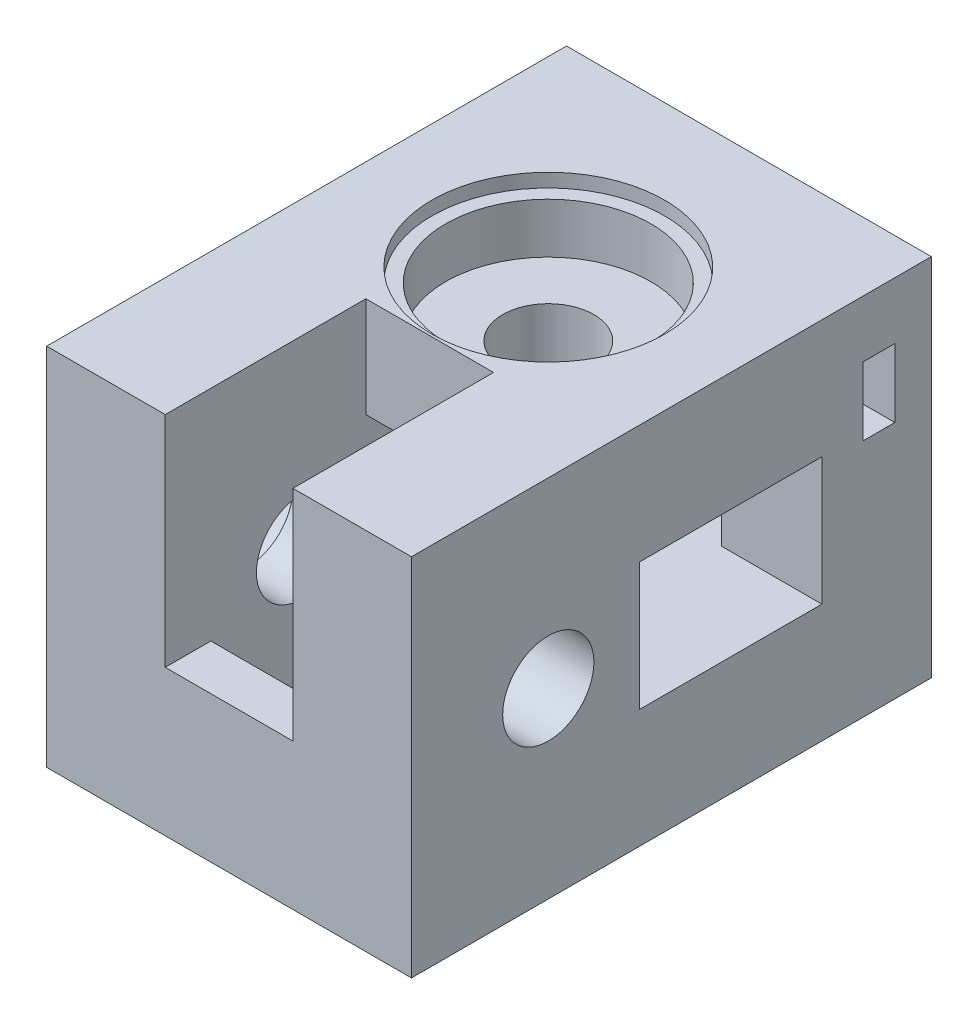
SolidWorks part; units mm, degrees
ref_plane "Plan de face" through (0, 0, 0) normal (0, 0, 1) x (1, 0, 0)
ref_plane "Plan de dessus" through (0, 0, 0) normal (0, 1, 0) x (1, 0, 0)
ref_plane "Plan de droite" through (0, 0, 0) normal (1, 0, 0) x (0, 0, -1)
sketch "Esquisse1" plane through (0, 0, 0) normal (0, 0, 1) x (1, 0, 0)
  line L1 (-40, 40) -> (0, 40)
  line L2 (-40, 40) -> (-40, 0)
  line L3 (-40, 0) -> (0, 0)
  line L4 (0, 40) -> (0, 0)
  dimension "D1" = 40
  dimension "D2" = 40
extrude "Boss.-Extru.1" add sketch "Esquisse1" along normal blind 50
sketch "Esquisse2" plane through (0, 40, 0) normal (0, 1, 0) x (1, 0, 0)
  line L0 (0, 0) -> (-40, 0) construction
  line L1 (-40, -50) -> (-40, 0) construction
  circle A0 centre (-20, -15) radius 5
  dimension "D1" = 10
  dimension "D2" = 15
  dimension "D3" = 20
extrude "Enlèv. mat.-Extru.1" cut sketch "Esquisse2" against normal through all
sketch "Esquisse3" plane through (-40, 0, 0) normal (-1, 0, 0) x (0, 0, 1)
  line L0 (50, 40) -> (50, 0) construction
  line L1 (50, 40) -> (0, 40) construction
  circle A0 centre (35, 20) radius 5
  dimension "D1" = 10
  dimension "D2" = 15
  dimension "D3" = 20
extrude "Enlèv. mat.-Extru.2" cut sketch "Esquisse3" against normal through all
sketch "Esquisse4" plane through (-40, 0, 0) normal (-1, 0, 0) x (0, 0, 1)
  line L1 (22, 27) -> (0, 27)
  line L2 (22, 27) -> (22, 13)
  line L3 (22, 13) -> (0, 13)
  line L4 (0, 27) -> (0, 13)
  line L5 (0, 40) -> (0, 0) construction
  line L6 (50, 0) -> (0, 0) construction
  line L7 (50, 40) -> (0, 40) construction
  dimension "D1" = 14
  dimension "D2" = 22
  dimension "D3" = 0
  dimension "D4" = 13
  dimension "D5" = 13
extrude "Enlèv. mat.-Extru.3" cut sketch "Esquisse4" against normal blind 29
sketch "Esquisse5" plane through (0, 0, 0) normal (0, -1, 0) x (1, 0, 0)
  line L0 (-40, 50) -> (0, 50) construction
  line L1 (-13, 25) -> (-27, 25)
  line L2 (-13, 25) -> (-13, 45)
  line L3 (-13, 45) -> (-27, 45)
  line L4 (-27, 25) -> (-27, 45)
  line L5 (-40, 50) -> (-40, 0) construction
  dimension "D1" = 20
  dimension "D2" = 5
  dimension "D3" = 14
  dimension "D4" = 13
extrude "Enlèv. mat.-Extru.4" cut sketch "Esquisse5" against normal blind 29
sketch "Esquisse6" plane through (0, 0, 0) normal (1, 0, 0) x (0, 0, -1)
  line L1 (-5, 27) -> (-25, 27)
  line L2 (0, 0) -> (0, 40) construction
  line L3 (-5, 13) -> (-25, 13)
  line L4 (-25, 27) -> (-25, 13)
  line L5 (-50, 0) -> (0, 0) construction
  line L6 (-5, 27) -> (-5, 13)
  dimension "D1" = 14
  dimension "D2" = 5
  dimension "D3" = 13
  dimension "D4" = 20
extrude "Enlèv. mat.-Extru.5" cut sketch "Esquisse6" against normal blind 24
sketch "Esquisse7" plane through (0, 40, 0) normal (0, 1, 0) x (1, 0, 0)
  line L0 (0, -50) -> (-40, -50) construction
  line L1 (-27, -50) -> (-13, -50)
  line L2 (-27, -50) -> (-27, -28)
  line L3 (-27, -28) -> (-13, -28)
  line L4 (-13, -50) -> (-13, -28)
  line L5 (-40, -50) -> (-40, 0) construction
  dimension "D1" = 14
  dimension "D2" = 22
  dimension "D3" = 13
extrude "Enlèv. mat.-Extru.6" cut sketch "Esquisse7" against normal blind 24
sketch "Esquisse10" plane through (0, 40, 0) normal (0, 1, 0) x (1, 0, 0)
  circle A0 centre (-20, -15) radius 11.25
  dimension "D1" = 22.5
extrude "Enlèv. mat.-Extru.9" cut sketch "Esquisse10" against normal blind 7
sketch "Esquisse11" plane through (0, 40, 0) normal (0, 1, 0) x (1, 0, 0)
  circle A0 centre (-20, -15) radius 12.75
  dimension "D1" = 25.5
extrude "Enlèv. mat.-Extru.10" cut sketch "Esquisse11" against normal blind 1.5
sketch "Esquisse14" plane through (-40, 0, 0) normal (-1, 0, 0) x (0, 0, 1)
  circle A0 centre (35, 20) radius 11.25
  dimension "D1" = 22.5
extrude "Enlèv. mat.-Extru.11" cut sketch "Esquisse14" against normal blind 7
sketch "Esquisse15" plane through (-40, 0, 0) normal (-1, 0, 0) x (0, 0, 1)
  circle A0 centre (35, 20) radius 12.75
  dimension "D1" = 25.5
extrude "Enlèv. mat.-Extru.12" cut sketch "Esquisse15" against normal blind 1.5
sketch "Esquisse16" plane through (0, 0, 0) normal (0, 0, -1) x (-1, 0, 0)
  line L1 (0, 40) -> (40, 40)
  line L2 (0, 40) -> (0, 0)
  line L3 (0, 0) -> (40, 0)
  line L4 (40, 40) -> (40, 0)
extrude "Boss.-Extru.2" add sketch "Esquisse16" along normal blind 7
sketch "Esquisse17" plane through (0, 0, -7) normal (0, 0, -1) x (-1, 0, 0)
  line L0 (40, 40) -> (0, 40) construction
  line L1 (40, 0) -> (40, 40) construction
  circle A0 centre (7.5, 30) radius 2.25
  circle A1 centre (30, 7.5) radius 2.25
  dimension "D1" = 4.5
  dimension "D2" = 4.5
  dimension "D3" = 32.5
  dimension "D4" = 32.5
  dimension "D5" = 10
  dimension "D6" = 10
extrude "Enlèv. mat.-Extru.13" cut sketch "Esquisse17" against normal blind 15
sketch "Esquisse18" plane through (0, 0, 0) normal (1, 0, 0) x (0, 0, -1)
  line L0 (7, 40) -> (7, 0) construction
  line L1 (3, 33.75) -> (-0.5, 33.75)
  line L2 (3, 33.75) -> (3, 26.25)
  line L3 (3, 26.25) -> (-0.5, 26.25)
  line L4 (-0.5, 33.75) -> (-0.5, 26.25)
  line L9 (-50, 40) -> (7, 40) construction
  dimension "D1" = 7.5
  dimension "D2" = 3.5
  dimension "D3" = 4
  dimension "D4" = 6.25
extrude "Enlèv. mat.-Extru.14" cut sketch "Esquisse18" against normal blind 12
sketch "Esquisse19" plane through (0, 0, 0) normal (0, -1, 0) x (1, 0, 0)
  line L0 (0, -7) -> (-40, -7) construction
  line L1 (-26.25, -3) -> (-33.75, -3)
  line L2 (-26.25, -3) -> (-26.25, 0.5)
  line L3 (-26.25, 0.5) -> (-33.75, 0.5)
  line L4 (-33.75, -3) -> (-33.75, 0.5)
  line L5 (-40, 50) -> (-40, -7) construction
  dimension "D1" = 7.5
  dimension "D2" = 3.5
  dimension "D3" = 4
  dimension "D4" = 6.25
extrude "Enlèv. mat.-Extru.15" cut sketch "Esquisse19" against normal blind 12
